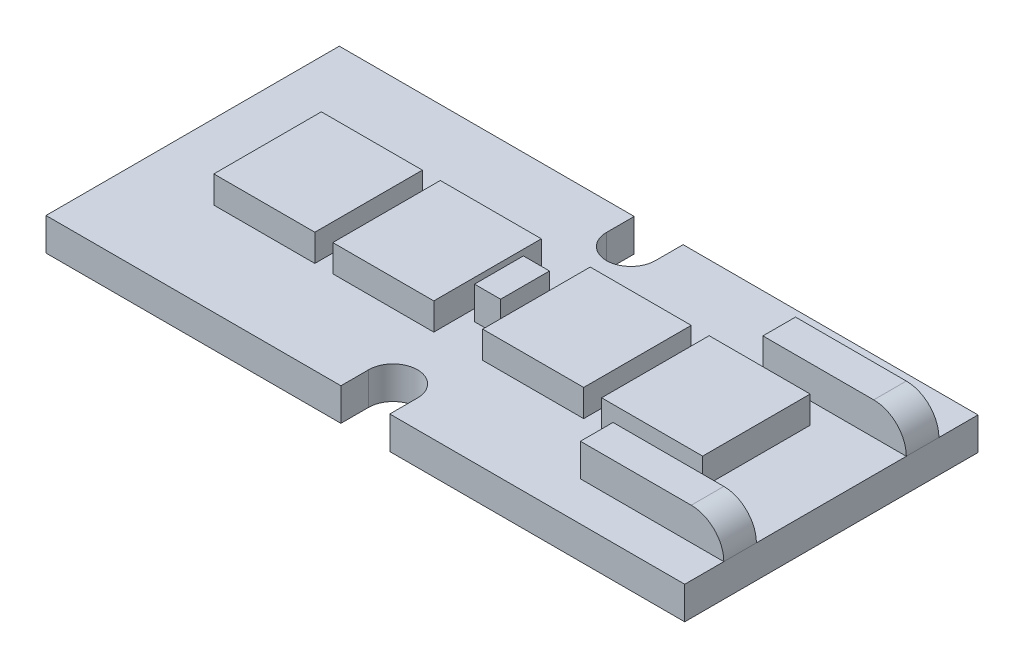
SolidWorks part; units mm, degrees
ref_plane "Front" through (0, 0, 0) normal (0, 0, 1) x (1, 0, 0)
ref_plane "Top" through (0, 0, 0) normal (0, 1, 0) x (1, 0, 0)
ref_plane "Right" through (0, 0, 0) normal (1, 0, 0) x (0, 0, -1)
sketch "草图1" plane through (0, 0, 0) normal (0, 1, 0) x (1, 0, 0)
  line L0 (0, -4.5) -> (33.4095, -4.5) construction
  line L1 (0, 0) -> (9.05, 0)
  line L2 (0, 0) -> (0, -9)
  line L3 (0, -9) -> (9.05, -9)
  line L4 (19.6, 0) -> (19.6, -9)
  line L5 (9.8, 0) -> (9.8, -15.73) construction
  line L6 (9.05, -8.15) -> (9.05, -9)
  line L7 (10.55, -8.15) -> (10.55, -9)
  line L8 (9.05, -0.85) -> (9.05, 0)
  line L9 (10.55, -0.85) -> (10.55, 0)
  line L12 (10.55, -9) -> (19.6, -9)
  line L13 (10.55, 0) -> (19.6, 0)
  circle A0 centre (9.8, -8.15) radius 0.75 construction
  circle A1 centre (9.8, -0.85) radius 0.75 construction
  arc A2 (10.55, -8.15) -> (9.05, -8.15) centre (9.8, -8.15) ccw
  arc A3 (9.05, -0.85) -> (10.55, -0.85) centre (9.8, -0.85) ccw
  dimension "D4" = 1.5
  dimension "D1" = 9
  dimension "D2" = 19.6
  dimension "D3" = 7.3
extrude "凸台-拉伸1" add sketch "草图1" along normal blind 1
sketch "草图2" plane through (0, 1, 0) normal (0, 1, 0) x (1, 0, 0)
  line L0 (0, -4.5) -> (22.2066, -4.5) construction
  line L1 (0, 0) -> (0, -9) construction
  line L6 (9.8, -1.6) -> (9.8, -7.4) construction
  line L7 (5.4, -6.15) -> (2.3, -6.15)
  line L8 (5.4, -6.15) -> (5.4, -2.85)
  line L9 (5.4, -2.85) -> (2.3, -2.85)
  line L10 (2.3, -6.15) -> (2.3, -2.85)
  line L11 (5.4, -6.15) -> (2.3, -2.85) construction
  line L12 (5.4, -2.85) -> (2.3, -6.15) construction
  line L13 (9.05, -6.15) -> (9.05, -2.85)
  line L14 (9.05, -6.15) -> (5.95, -6.15)
  line L15 (5.95, -6.15) -> (5.95, -2.85)
  line L16 (9.05, -2.85) -> (5.95, -2.85)
  line L17 (10.55, -6.15) -> (13.65, -6.15)
  line L18 (13.65, -6.15) -> (13.65, -2.85)
  line L19 (10.55, -2.85) -> (13.65, -2.85)
  line L20 (10.55, -6.15) -> (10.55, -2.85)
  line L21 (14.2, -2.85) -> (17.3, -2.85)
  line L22 (17.3, -6.15) -> (17.3, -2.85)
  line L23 (14.2, -6.15) -> (17.3, -6.15)
  line L24 (14.2, -6.15) -> (14.2, -2.85)
  line L25 (9.05, -0.85) -> (9.05, -8.15) construction
  arc A0 (9.05, -0.85) -> (10.55, -0.85) centre (9.8, -0.85) ccw construction
  arc A1 (10.55, -8.15) -> (9.05, -8.15) centre (9.8, -8.15) ccw construction
  point P4 (3.85, -4.5)
  dimension "D1" = 3.3
  dimension "D3" = 15
  dimension "D4" = 3.1
  dimension "D2" = 2
extrude "凸台-拉伸2" add sketch "草图2" along normal blind 0.83
sketch "草图3" plane through (0, 1, 0) normal (0, 1, 0) x (1, 0, 0)
  line L0 (9.8, -1.6) -> (9.8, -7.4) construction
  line L1 (0, -4.5) -> (19.6, -4.5) construction
  line L2 (0, 0) -> (0, -9) construction
  line L3 (19.6, -9) -> (19.6, 0) construction
  line L4 (19.6, -6.8) -> (15.2, -6.8)
  line L5 (9.4, -5.25) -> (10.2, -5.25)
  line L6 (9.4, -5.25) -> (9.4, -3.75)
  line L7 (9.4, -3.75) -> (10.2, -3.75)
  line L8 (10.2, -5.25) -> (10.2, -3.75)
  line L9 (9.4, -5.25) -> (10.2, -3.75) construction
  line L10 (9.4, -3.75) -> (10.2, -5.25) construction
  line L11 (19.6, -1.2) -> (15.2, -1.2)
  line L12 (19.6, -1.2) -> (19.6, -2.2)
  line L13 (19.6, -2.2) -> (15.2, -2.2)
  line L14 (15.2, -1.2) -> (15.2, -2.2)
  line L15 (15.2, -7.8) -> (15.2, -6.8)
  line L16 (19.6, -7.8) -> (15.2, -7.8)
  line L17 (19.6, -7.8) -> (19.6, -6.8)
  arc A0 (9.05, -0.85) -> (10.55, -0.85) centre (9.8, -0.85) ccw construction
  arc A1 (10.55, -8.15) -> (9.05, -8.15) centre (9.8, -8.15) ccw construction
  point P16 (9.8, -4.5)
  dimension "D1" = 0.8
  dimension "D2" = 1.5
  dimension "D3" = 4.4
  dimension "D4" = 2.3
  dimension "D5" = 1
extrude "凸台-拉伸3" add sketch "草图3" along normal blind 1
fillet "圆角1" radius 1 2 edges at (19.6, 2, 7.3) (19.6, 2, 1.7)
